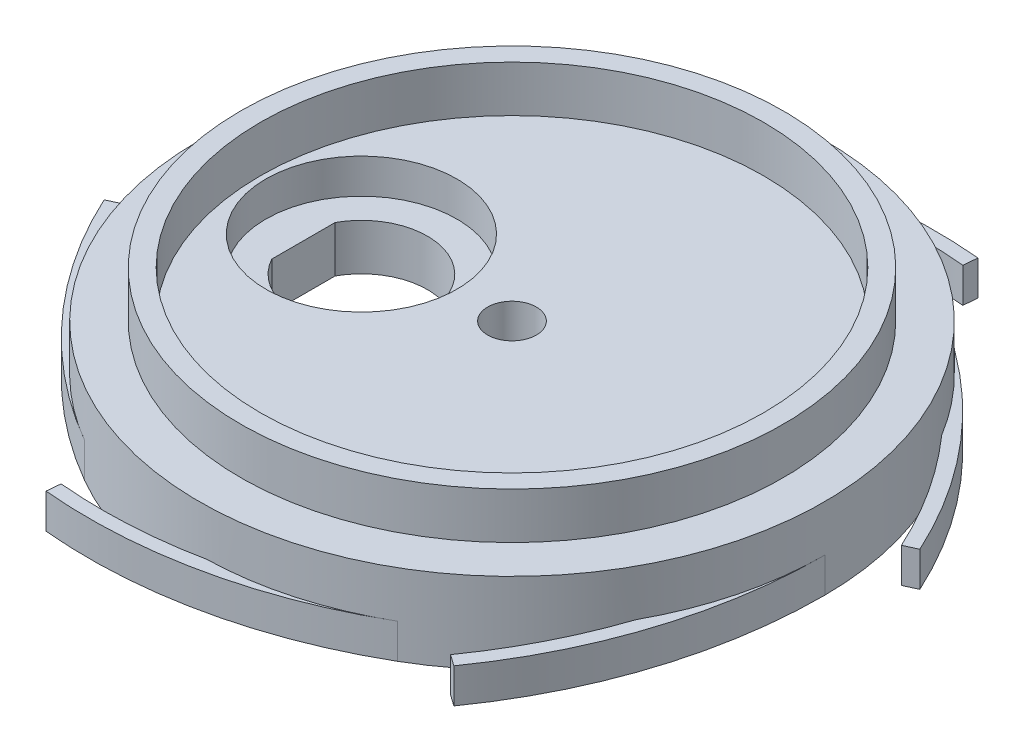
SolidWorks part; units mm, degrees
material "ABS"
ref_plane "Front" through (0, 0, 0) normal (0, 0, 1) x (1, 0, 0)
ref_plane "Top" through (0, 0, 0) normal (0, 1, 0) x (1, 0, 0)
ref_plane "Right" through (0, 0, 0) normal (1, 0, 0) x (0, 0, -1)
sketch "Sketch1" plane through (0, 0, 0) normal (0, 0, 1) x (1, 0, 0)
  line L0 (0, 0) -> (-23.425, 0) construction
  line L1 (-23.425, 0) -> (-23.425, -4)
  line L4 (-27, -8) -> (0, -8)
  line L5 (0, -8) -> (0, 0) construction
  line L6 (0, 0) -> (0, -8) construction
  line L8 (-27, -8) -> (-27, -4)
  line L9 (-27, -4) -> (-23.425, -4)
  line L10 (0, -8) -> (0, -19.7735) construction
  line L11 (-21.7215, 0) -> (-21.7215, -4)
  line L12 (-21.7215, -4) -> (0, -4)
  line L13 (-21.7215, 0) -> (-23.425, 0)
  line L14 (0, -8) -> (0, -4)
  dimension "D1" = 54
  dimension "D2" = 8
  dimension "D3" = 4
  dimension "D6" = 23.425
revolve "Revolve1" add sketch "Sketch1" angle 360 about L10
sketch "Sketch18" plane through (0, -8, 0) normal (0, -1, 0) x (1, 0, 0)
  line L0 (-15, 0) -> (19.2667, 24.2857) construction
  line L1 (18.2876, 23.5918) -> (19.2667, 24.2857)
  line L2 (13.5, 23.3827) -> (0, 0) construction
  line L3 (0, 0) -> (27, 0) construction
  line L4 (29.5749, -4.0416) -> (30.6654, -4.5426)
  line L5 (11.2873, -27.6335) -> (11.3987, -28.8283)
  line L6 (-18.2876, -23.5918) -> (-19.2667, -24.2857)
  line L7 (-29.5749, 4.0416) -> (-30.6654, 4.5426)
  line L8 (-11.2873, 27.6335) -> (-11.3987, 28.8283)
  circle A0 centre (0, 0) radius 27 construction
  arc A2 (23.688, 12.9568) -> (18.2876, 23.5918) centre (-15, 0) ccw
  arc A3 (27, 0) -> (19.2667, 24.2857) centre (-15, 0) ccw
  arc A4 (23.688, 12.9568) -> (13.5, 23.3827) centre (0, 0) ccw
  arc A5 (23.0649, -14.036) -> (27, 0) centre (0, 0) ccw
  arc A6 (23.0649, -14.036) -> (29.5749, -4.0416) centre (-7.5, 12.9904) ccw
  arc A7 (13.5, -23.3827) -> (30.6654, -4.5426) centre (-7.5, 12.9904) ccw
  arc A8 (-0.6231, -26.9928) -> (13.5, -23.3827) centre (0, 0) ccw
  arc A9 (-0.6231, -26.9928) -> (11.2873, -27.6335) centre (7.5, 12.9904) ccw
  arc A10 (-13.5, -23.3827) -> (11.3987, -28.8283) centre (7.5, 12.9904) ccw
  arc A11 (-23.688, -12.9568) -> (-13.5, -23.3827) centre (0, 0) ccw
  arc A12 (-23.688, -12.9568) -> (-18.2876, -23.5918) centre (15, 0) ccw
  arc A13 (-27, 0) -> (-19.2667, -24.2857) centre (15, 0) ccw
  arc A14 (-23.0649, 14.036) -> (-27, 0) centre (0, 0) ccw
  arc A15 (-23.0649, 14.036) -> (-29.5749, 4.0416) centre (7.5, -12.9904) ccw
  arc A16 (-13.5, 23.3827) -> (-30.6654, 4.5426) centre (7.5, -12.9904) ccw
  arc A17 (0.6231, 26.9928) -> (-13.5, 23.3827) centre (0, 0) ccw
  arc A18 (0.6231, 26.9928) -> (-11.2873, 27.6335) centre (-7.5, -12.9904) ccw
  arc A19 (13.5, 23.3827) -> (-11.3987, 28.8283) centre (-7.5, -12.9904) ccw
  dimension "D1" = 1.2
  dimension "D2" = 15
  dimension "D3" = 60
  dimension "D4" = 31
  dimension "D5" = 27
  dimension "D6" = 1.2
extrude "Boss-Extrude1" add sketch "Sketch18" along normal blind 3
hole_wizard "Ø4.2 (4.2) Diameter Hole1" positions "Sketch21" profile "Sketch23" hole size "Ø4.2" standard "GB" end condition through all
sketch "Sketch21" plane through (0, -4, 0) normal (0, 1, 0) x (1, 0, 0)
  point P0 (0, 0)
sketch "Sketch23" plane through (0, -4, 0) normal (1, 0, 0) x (0, 0, 1)
  line L0 (0, 0) -> (0, 7)
  line L1 (0, 7) -> (2.1, 7)
  line L2 (2.1, 7) -> (2.1, 0)
  line L5 (2.1, 0) -> (0, 0)
  line L11 (0, -6.35) -> (0, 107.95) construction
  dimension "Thru Hole Dia." = 4.2
  dimension "Thru Hole Depth" = 7
sketch "Sketch24" plane through (0, -11, 0) normal (0, -1, 0) x (1, 0, 0)
  line L0 (-18, 2.7368) -> (-18, -2.7368)
  circle A0 centre (-13, 0) radius 5.7
  circle A1 centre (20, 0) radius 1
  dimension "D1" = 11.4
  dimension "D4" = 2
  dimension "D2" = 13
  dimension "D3" = 10.7
  dimension "D5" = 20
extrude "Cut-Extrude3" cut sketch "Sketch24" against normal blind 10 contours L0 A0 | A1
sketch "Sketch25" plane through (0, -4, 0) normal (0, 1, 0) x (1, 0, 0)
  circle A0 centre (-13, 0) radius 8.25
  dimension "D2" = 16.5
  dimension "D1" = 13
extrude "Cut-Extrude4" cut sketch "Sketch25" against normal blind 3
